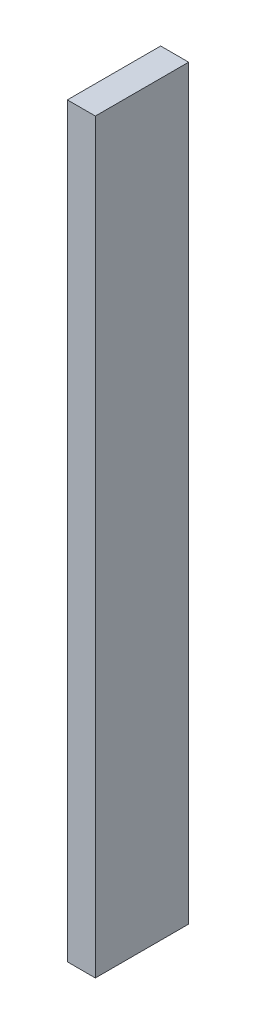
SolidWorks part; units mm, degrees
ref_plane "Front Plane" through (0, 0, 0) normal (0, 0, 1) x (1, 0, 0)
ref_plane "Top Plane" through (0, 0, 0) normal (0, 1, 0) x (1, 0, 0)
ref_plane "Right Plane" through (0, 0, 0) normal (1, 0, 0) x (0, 0, -1)
sketch "Sketch2" plane through (0, 0, 0) normal (0, 1, 0) x (1, 0, 0)
  line L1 (-1.5, 5) -> (1.5, 5)
  line L2 (-1.5, 5) -> (-1.5, -5)
  line L3 (-1.5, -5) -> (1.5, -5)
  line L4 (1.5, 5) -> (1.5, -5)
  line L5 (-1.5, 5) -> (1.5, -5) construction
  line L6 (-1.5, -5) -> (1.5, 5) construction
  point P0 (0, 0)
  dimension "D1" = 10
  dimension "D2" = 3
extrude "Boss-Extrude1" add sketch "Sketch2" along normal blind 80
